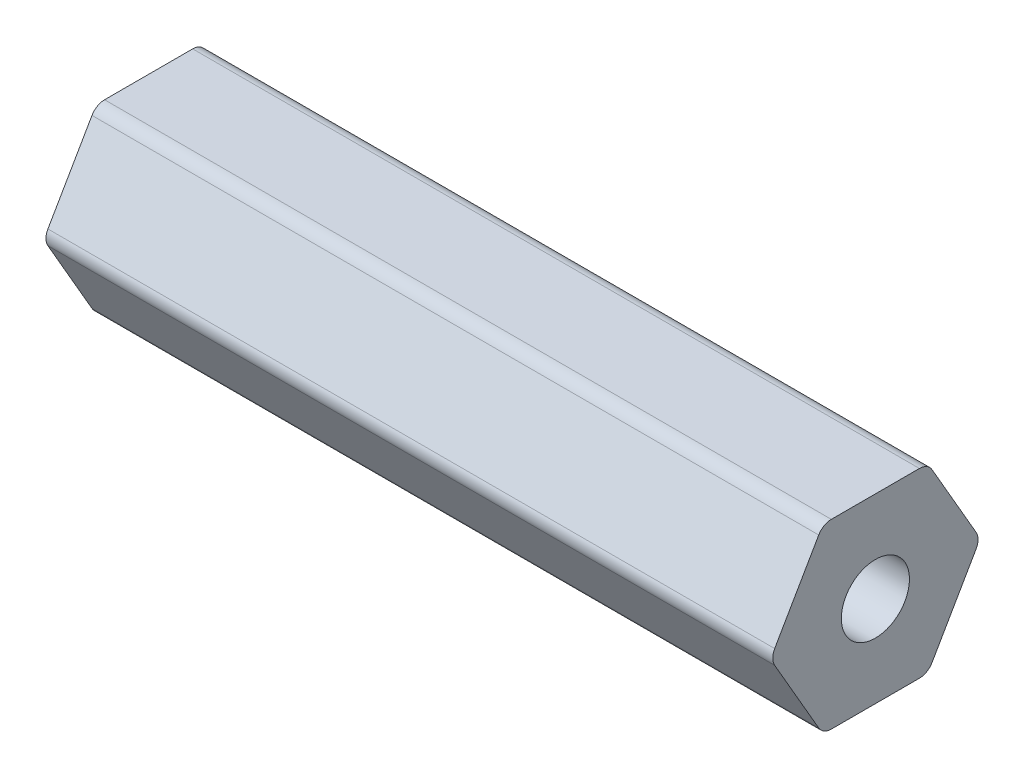
SolidWorks part; units mm, degrees
material "7075-T6 (SN)"
ref_plane "Front Plane" through (0, 0, 0) normal (0, 0, 1) x (1, 0, 0)
ref_plane "Top Plane" through (0, 0, 0) normal (0, 1, 0) x (1, 0, 0)
ref_plane "Right Plane" through (0, 0, 0) normal (1, 0, 0) x (0, 0, -1)
sketch "Sketch1" plane through (0, 0, 0) normal (1, 0, 0) x (0, 0, -1)
  line L1 (7.0391, 0.508) -> (3.9595, 5.842)
  line L2 (3.0796, 6.35) -> (-3.0796, 6.35)
  line L3 (-3.9595, 5.842) -> (-7.0391, 0.508)
  line L4 (-7.0391, -0.508) -> (-3.9595, -5.842)
  line L5 (-3.0796, -6.35) -> (3.0796, -6.35)
  line L6 (3.9595, -5.842) -> (7.0391, -0.508)
  circle A0 centre (0, 0) radius 6.35 construction
  arc A1 (3.0796, 6.35) -> (3.9595, 5.842) centre (3.0796, 5.334) cw
  arc A2 (7.0391, 0.508) -> (7.0391, -0.508) centre (6.1592, 0) cw
  arc A3 (3.9595, -5.842) -> (3.0796, -6.35) centre (3.0796, -5.334) cw
  arc A4 (-3.0796, -6.35) -> (-3.9595, -5.842) centre (-3.0796, -5.334) cw
  arc A5 (-7.0391, -0.508) -> (-7.0391, 0.508) centre (-6.1592, 0) cw
  arc A6 (-3.9595, 5.842) -> (-3.0796, 6.35) centre (-3.0796, 5.334) cw
  circle A7 centre (0, 0) radius 2.3813
  point P11 (3.6662, 6.35)
  point P14 (7.3323, 0)
  dimension "D1" = 12.7
  dimension "D3" = 1.016
  dimension "D4" = 4.7625
  dimension "D2" = 6.35
extrude "Boss-Extrude1" add sketch "Sketch1" along normal blind 50.8
